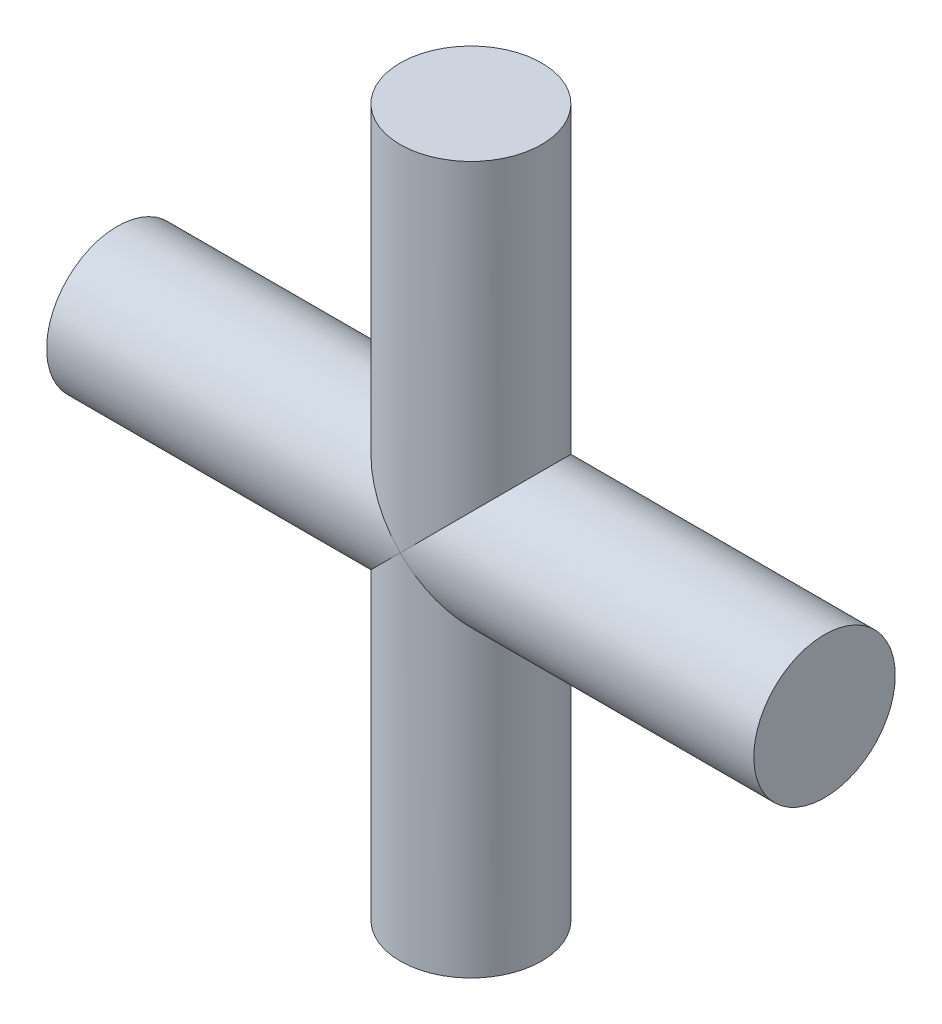
SolidWorks part; units mm, degrees
ref_plane "Ebene vorne" through (0, 0, 0) normal (0, 0, 1) x (1, 0, 0)
ref_plane "Ebene oben" through (0, 0, 0) normal (0, 1, 0) x (1, 0, 0)
ref_plane "Ebene rechts" through (0, 0, 0) normal (1, 0, 0) x (0, 0, -1)
sketch "Skizze2" plane through (0, 0, 0) normal (0, 1, 0) x (1, 0, 0)
  circle A0 centre (0, 0) radius 1
  dimension "D1" = 2
extrude "Aufsatz-Linear austragen1" add sketch "Skizze2" along normal mid plane 10
sketch "Skizze3" plane through (0, 0, 0) normal (1, 0, 0) x (0, 0, -1)
  line L0 (-1, 5) -> (-1, -5) construction
  circle A0 centre (0, 0) radius 1
  point P3 (-1, 0)
extrude "Aufsatz-Linear austragen2" add sketch "Skizze3" along normal mid plane 10
